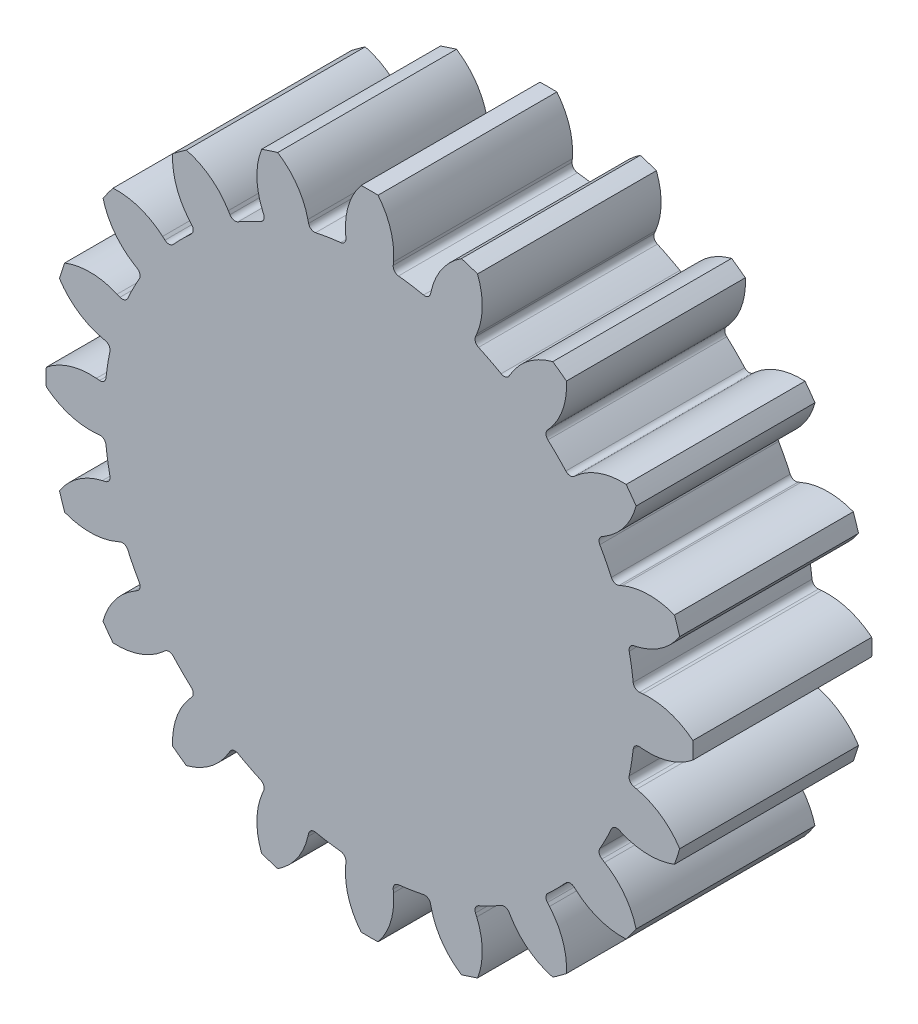
SolidWorks part; units mm, degrees
ref_plane "Front Plane" through (0, 0, 0) normal (0, 0, 1) x (1, 0, 0)
ref_plane "Top Plane" through (0, 0, 0) normal (0, 1, 0) x (1, 0, 0)
ref_plane "Right Plane" through (0, 0, 0) normal (1, 0, 0) x (0, 0, -1)
sketch "Sketch1" plane through (0, 0, 0) normal (0, 0, 1) x (1, 0, 0)
  line L0 (0, 0) -> (14.4994, 0) construction
  line L1 (0, 0) -> (14.6758, 2.3244) construction
  line L2 (0, 0) -> (14.1374, 1.2369) construction
  line L3 (0, 0) -> (13.6777, 0.3582) construction
  line L4 (9.165, 0.8018) -> (8.8625, 0.7754)
  line L5 (8.7868, 1.3917) -> (0, 0)
  line L6 (9.165, -0.8018) -> (8.8625, -0.7754)
  line L7 (8.7868, -1.3917) -> (0, 0)
  circle A0 centre (0, 0) radius 10.85 construction
  circle A1 centre (0, 0) radius 9.2 construction
  circle A2 centre (0, 0) radius 8.9 construction
  arc A3 (9.165, 0.8018) -> (10.8463, 0.284) centre (9.3686, -1.5255) cw
  arc A4 (8.8625, 0.7754) -> (8.7868, 1.3917) centre (0, 0) ccw
  arc A5 (10.8463, 0.284) -> (10.8463, -0.284) centre (0, 0) cw
  arc A6 (9.165, -0.8018) -> (10.8463, -0.284) centre (9.3686, 1.5255) ccw
  arc A7 (8.8625, -0.7754) -> (8.7868, -1.3917) centre (0, 0) cw
  dimension "D1" = 21.7
  dimension "D2" = 18.4
  dimension "D3" = 17.8
  dimension "D4" = 9
  dimension "D5" = 5
  dimension "D6" = 1.5
extrude "Boss-Extrude2" add sketch "Sketch1" along normal blind 6
fillet "Fillet3" radius 0.2 1 edges at (8.8625, 0.7754, 3)
fillet "Fillet4" radius 0.2 1 edges at (8.8625, -0.7754, 3)
pattern_circular "CirPattern2" count 20 over 360 about axis through (0, 0, 0) along (0, 0, 1) of "Boss-Extrude2", "Fillet3", "Fillet4"
